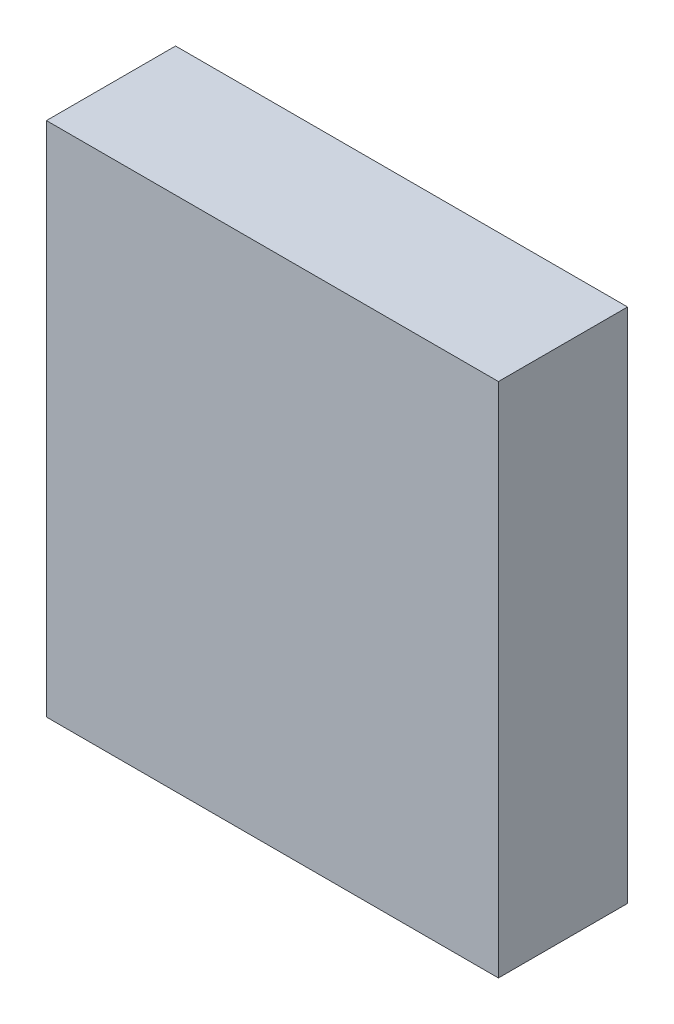
SolidWorks part; units mm, degrees
material "1023 al carbonio, lamiera (SS)"
ref_plane "Piano frontale" through (0, 0, 0) normal (0, 0, 1) x (1, 0, 0)
ref_plane "Piano superiore" through (0, 0, 0) normal (0, 1, 0) x (1, 0, 0)
ref_plane "Piano destro" through (0, 0, 0) normal (1, 0, 0) x (0, 0, -1)
sketch "Schizzo1" plane through (0, 0, 0) normal (0, 0, 1) x (1, 0, 0)
  line L0 (17.5, 40) -> (17.5, 0) construction
  line L1 (0, 0) -> (35, 0)
  line L2 (0, 0) -> (0, 40)
  line L3 (0, 40) -> (35, 40)
  line L4 (35, 0) -> (35, 40)
  dimension "D1" = 40
  dimension "D2" = 35
extrude "Estrusione-Estrusione1" add sketch "Schizzo1" along normal blind 10
